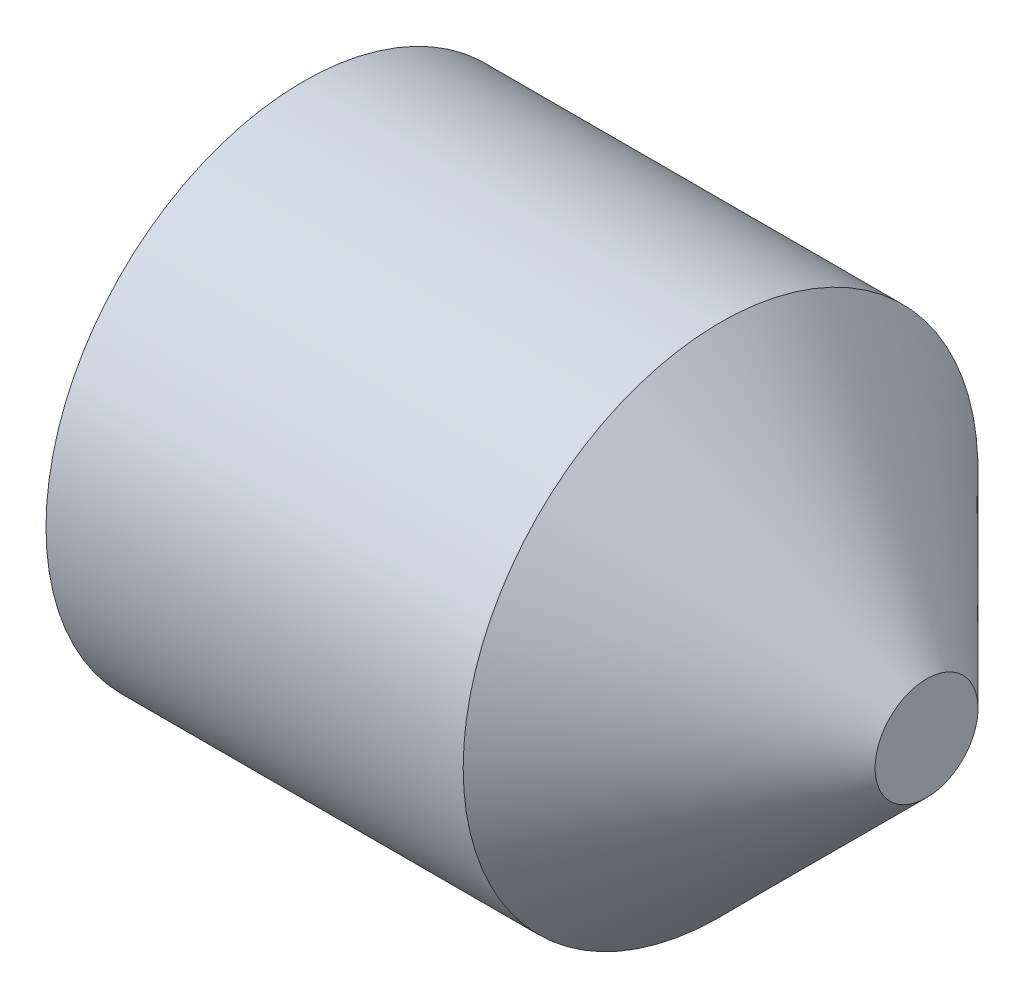
SolidWorks part; units mm, degrees
revolve "BaseBody" add sketch "BodySke" angle 360 about L5
sketch "BodySke" plane through (0, 0, 0) normal (0, 0, 1) x (1, 0, 0)
  line L0 (0, 0) -> (0, 10.352)
  line L1 (0, 10.352) -> (0.9515, 12)
  line L2 (0.9515, 12) -> (20.4, 12)
  line L3 (30, 0) -> (30, 2.4)
  line L4 (30, 0) -> (0, 0)
  line L5 (-12.7, 0) -> (88.9, 0) construction
  line L6 (30, 2.4) -> (20.4, 12)
  line L7 (3, 15.875) -> (3, -3.175) construction
  line L8 (0, -10.352) -> (0.9515, -12) construction
  line L9 (30, -2.4) -> (20.4, -12) construction
  dimension "Drive_ch_ang" = 60
  dimension "Cone_ang" = 90
cosmetic thread "ThreadCosmetic" [suppressed] parameters "Thread_minor"=20.704
ref_plane "Plane1" through (0, 0, 0) normal (0, 0, 1) x (1, 0, 0)
ref_plane "Plane2" through (0, 0, 0) normal (0, 1, 0) x (1, 0, 0)
ref_plane "Plane3" through (0, 0, 0) normal (1, 0, 0) x (0, 0, -1)
other "Configuration Table"
sketch "Sketch2" plane through (0, 0, 0) normal (-1, 0, 0) x (0, 0, 1)
  line L0 (3.4641, 6) -> (-3.4641, 6)
  line L1 (-3.4641, 6) -> (-6.9282, 0)
  line L2 (3.4641, 6) -> (6.9282, 0)
  line L3 (3.4641, -6) -> (6.9282, 0)
  line L4 (3.4641, -6) -> (-3.4641, -6)
  line L5 (-3.4641, -6) -> (-6.9282, 0)
extrude "Hex" cut sketch "Sketch2" against normal blind 10
sketch "Sketch4" plane through (0, 4.7709, -0.5249) normal (-1, 0, 0) x (0, 0, 1)
  line L0 (0.5249, -4.7709) -> (10.6976, -4.7709)
  line L1 (0.5249, -4.7709) -> (6.6732, -1.2211) construction
  line L2 (0.5249, -4.7709) -> (5.6112, 4.0389)
  line L3 (8.9666, -2.6687) -> (10.2861, -1.9069)
  line L4 (6.5663, 1.4888) -> (7.8858, 2.2506)
  arc A0 (8.9666, -2.6687) -> (6.5663, 1.4888) centre (0.5249, -4.7709) ccw
  arc A1 (10.6976, -4.7709) -> (10.2861, -1.9069) centre (0.5249, -4.7709) ccw
  arc A2 (5.6112, 4.0389) -> (7.8858, 2.2506) centre (0.5249, -4.7709) cw
  circle A3 centre (0.5249, -4.7709) radius 8.6995 construction
  circle A4 centre (0.5249, -4.7709) radius 10.1727 construction
  dimension "D1" = 30
  dimension "Spline_a_dim" = 60
extrude "Spline6" [suppressed] cut sketch "Sketch4" against normal blind 12
pattern_circular "CirPattern1" [suppressed] count 6 every 60 about axis through (-12.7, 0, 0) along (1, 0, 0)
sketch "Sketch5" plane through (0, 1.4735, 6.925) normal (-1, 0, 0) x (0, 0, 1)
  line L0 (-6.925, -1.4735) -> (3.2477, -1.4735)
  line L1 (-6.925, -1.4735) -> (-1.9049, 3.5466) construction
  line L2 (-6.925, -1.4735) -> (-6.925, 8.6992)
  line L3 (0.9237, 2.9807) -> (1.7623, 3.8193)
  line L4 (-2.4708, 6.3752) -> (-1.6322, 7.2139)
  line L5 (-2.4708, 6.3752) -> (0.9237, 2.9807)
  arc A1 (3.2477, -1.4735) -> (1.7623, 3.8193) centre (-6.925, -1.4735) ccw
  arc A2 (-6.925, 8.6992) -> (-1.6322, 7.2139) centre (-6.925, -1.4735) cw
  circle A3 centre (-6.925, -1.4735) radius 8.6995 construction
  circle A4 centre (-6.925, -1.4735) radius 10.1727 construction
  dimension "D1" = 45
  dimension "Spline_a_dim" = 90
extrude "Spline4" [suppressed] cut sketch "Sketch5" against normal blind 12
pattern_circular "CirPattern2" [suppressed] count 4 every 90 about axis through (-12.7, 0, 0) along (1, 0, 0)
sketch "ThdSchSke" plane through (0, 0, 0) normal (0, 0, 1) x (1, 0, 0)
  line L0 (0.9515, -10.352) -> (-0.2025, -12)
  line L1 (0.9515, -10.352) -> (2.1054, -12)
  line L2 (2.1054, -12) -> (2.1054, -15)
  line L3 (-3.175, 0) -> (5.1513, 0) construction
  line L4 (0.9515, 12) -> (0.9515, -12) construction
  line L5 (2.1054, -15) -> (-0.2025, -15)
  line L6 (-0.2025, -15) -> (-0.2025, -12)
revolve "ThreadSchematic" [suppressed] cut sketch "ThdSchSke" angle 360 about L3
pattern_linear "ThdSchPat" [suppressed]
equation "\"D2@Sketch2\" = \"Hex_size@Sketch2\" / 2"
equation "\"D3@Sketch2\" = \"Hex_size@Sketch2\" / 2"
equation "\"Thread_minor@ThreadCosmetic\" = \"Minor_dia@BodySke\""
equation "\"D1@Sketch4\" = \"Spline_a_dim@Sketch4\" / 2"
equation "\"D3@Sketch4\" = \"Spline_p_dim@Sketch4\" / 2"
equation "\"D2@CirPattern1\" = \"Spline_a_dim@Sketch4\""
equation "\"Num_teeth@CirPattern1\" = 360 / \"D2@CirPattern1\""
equation "\"Spline_a_dim@Sketch5\" = 90"
equation "\"Spline_p_dim@Sketch5\" = \"Spline_p_dim@Sketch4\""
equation "\"Spline_m_dim@Sketch5\" = \"Spline_m_dim@Sketch4\""
equation "\"Spline_n_dim@Sketch5\" = \"Spline_n_dim@Sketch4\""
equation "\"D1@Sketch5\" = \"Spline_a_dim@Sketch5\" / 2"
equation "\"D3@Sketch5\" = \"Spline_p_dim@Sketch5\" / 2"
equation "\"Key_eng@Spline4\" = \"Key_eng@Spline6\""
equation "\"Thread_minor@ThdSchSke\" = \"Thread_minor@ThreadCosmetic\""
equation "\"Diameter@ThdSchSke\" = \"Diameter@BodySke\""
equation "\"Overcut@ThdSchSke\" = \"Diameter@BodySke\" * 1.25"
equation "\"Num_threads@ThdSchPat\" = int( (\"Length@BodySke\" - ( ( ( \"Diameter@BodySke\" - \"Minor_dia@BodySke\" ) * 0.5 ) / tan( \"Drive_ch_ang@BodySke\" * 0.017453292 ) ) - ( ( \"Diameter@BodySke\" * 0.5 ) / tan( \"Cone_ang@BodySke\" * 0.008726646 ) ) ) / \"Advance@BodySke\" + 0.999 )  + 1"
equation "\"Num_threads@ThdSchPat\" = int( (\"Length@BodySke\" - ( ( ( \"Diameter@BodySke\" - \"Minor_dia@BodySke\" ) * 0.5 ) / tan( \"Drive_ch_ang@BodySke\" * 0.017453292 ) ) - ( (( \"Diameter@BodySke\" - \"Tip_dia@BodySke\") * 0.5 ) / tan( \"Cone_ang@BodySke\" * 0.008726646 ) ) ) / \"Advance@BodySke\" + 0.999 )  + 1"
equation "\"Advance@ThdSchPat\" = (\"Length@BodySke\" - ( ( ( \"Diameter@BodySke\" - \"Minor_dia@BodySke\" ) * 0.5 ) / tan( \"Drive_ch_ang@BodySke\" * 0.017453292 ) ) - ( ( \"Diameter@BodySke\" * 0.5 ) / tan( \"Cone_ang@BodySke\" * 0.008726646 ) ) ) /  (\"Num_threads@ThdSchPat\" - 1) 'relax it"
equation "\"Advance@ThdSchPat\" = (\"Length@BodySke\" - ( ( ( \"Diameter@BodySke\" - \"Minor_dia@BodySke\" ) * 0.5 ) / tan( \"Drive_ch_ang@BodySke\" * 0.017453292 ) ) - ( ( (\"Diameter@BodySke\" - \"Tip_dia@BodySke\") * 0.5 ) / tan( \"Cone_ang@BodySke\" * 0.008726646 ) ) ) /  (\"Num_threads@ThdSchPat\" - 1) 'relax it"
equation "' \"Num_threads@ThdSchPat\" = \"Num_threads@ThdSchPat\" - sgn( \"Num_threads@ThdSchPat\" - 1) '---chamfered tips only---"
